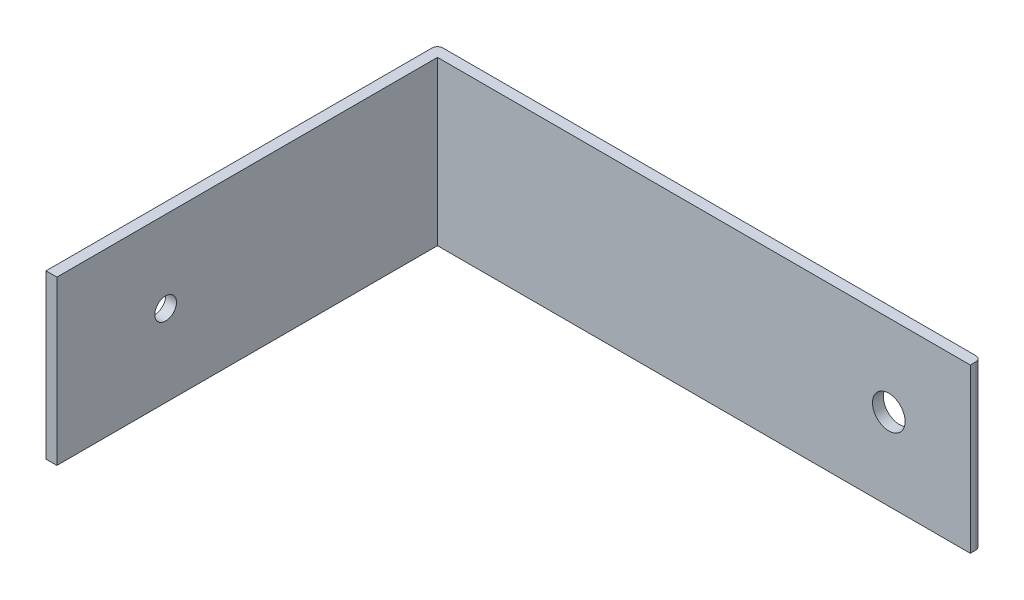
SolidWorks part; units mm, degrees
ref_plane "Plan de face" through (0, 0, 0) normal (0, 0, 1) x (1, 0, 0)
ref_plane "Plan de dessus" through (0, 0, 0) normal (0, 1, 0) x (1, 0, 0)
ref_plane "Plan de droite" through (0, 0, 0) normal (1, 0, 0) x (0, 0, -1)
sketch "Esquisse1" plane through (0, 0, 0) normal (0, 0, 1) x (1, 0, 0)
  line L1 (0, 0) -> (100, 0)
  line L2 (0, 0) -> (0, -30)
  line L3 (0, -30) -> (100, -30)
  line L4 (100, 0) -> (100, -30)
  dimension "D1" = 100
  dimension "D2" = 30
extrude "Boss.-Extru.1" add sketch "Esquisse1" along normal blind 2
sketch "Esquisse2" plane through (0, 0, 2) normal (0, 0, 1) x (1, 0, 0)
  line L0 (0, -30) -> (100, -30) construction
  line L1 (0, 0) -> (2, 0)
  line L2 (0, 0) -> (0, -30)
  line L3 (0, -30) -> (2, -30)
  line L4 (2, 0) -> (2, -30)
  dimension "D1" = 2
extrude "Boss.-Extru.2" add sketch "Esquisse2" along normal blind 70
sketch "Esquisse4" plane through (0, 0, 0) normal (-1, 0, 0) x (0, 0, 1)
  line L0 (72, 0) -> (72, -30) construction
  line L1 (72, -30) -> (0, -30) construction
  circle A0 centre (52, -15) radius 2
  dimension "D3" = 4
  dimension "D1" = 20
  dimension "D2" = 15
extrude "Enlèv. mat.-Extru.1" cut sketch "Esquisse4" against normal through all
fillet "Congé1" radius 1 1 edges at (0, -15, 0)
fillet "Congé2" radius 1 1 edges at (100, -15, 0)
sketch "Esquisse5" plane through (0, 0, 0) normal (0, 0, -1) x (-1, 0, 0)
  line L0 (0, 0) -> (0, -30) construction
  line L1 (-1, -30) -> (-99, -30) construction
  circle A0 centre (-85, -15) radius 3
  dimension "D1" = 6
  dimension "D2" = 85
  dimension "D3" = 15
extrude "Enlèv. mat.-Extru.2" cut sketch "Esquisse5" against normal blind 10
